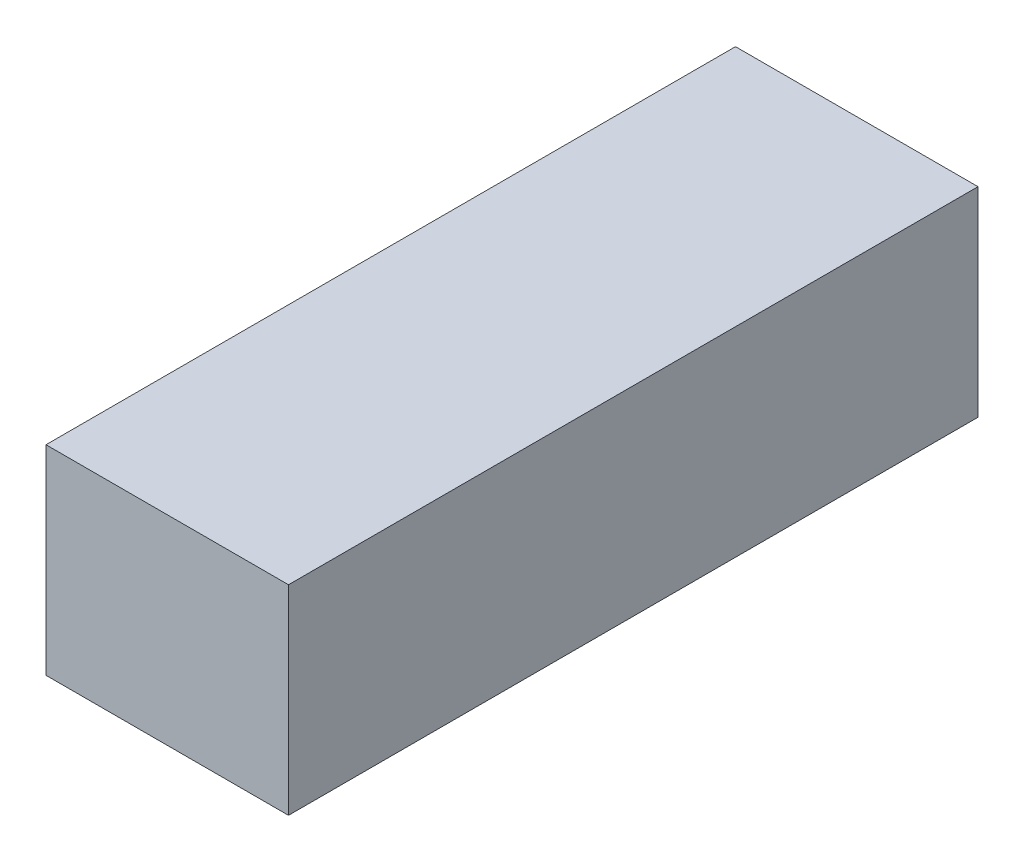
SolidWorks part; units mm, degrees
ref_plane "Front Plane" through (0, 0, 0) normal (0, 0, 1) x (1, 0, 0)
ref_plane "Top Plane" through (0, 0, 0) normal (0, 1, 0) x (1, 0, 0)
ref_plane "Right Plane" through (0, 0, 0) normal (1, 0, 0) x (0, 0, -1)
sketch "Sketch1" plane through (0, 0, 0) normal (0, 0, 1) x (1, 0, 0)
  line L1 (-25.5, -21) -> (25.5, -21)
  line L2 (-25.5, -21) -> (-25.5, 21)
  line L3 (-25.5, 21) -> (25.5, 21)
  line L4 (25.5, -21) -> (25.5, 21)
  line L5 (-25.5, -21) -> (25.5, 21) construction
  line L6 (-25.5, 21) -> (25.5, -21) construction
  point P0 (0, 0)
  dimension "D1" = 51
  dimension "D2" = 42
extrude "Boss-Extrude1" add sketch "Sketch1" along normal blind 145
